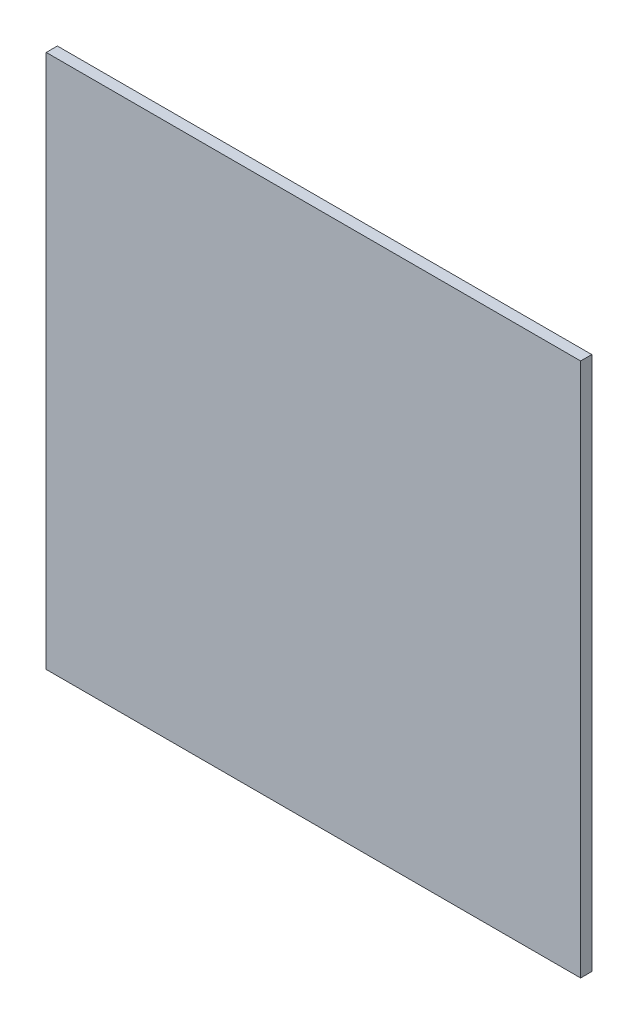
SolidWorks part; units mm, degrees
ref_plane "Front Plane" through (0, 0, 0) normal (0, 0, 1) x (1, 0, 0)
ref_plane "Top Plane" through (0, 0, 0) normal (0, 1, 0) x (1, 0, 0)
ref_plane "Right Plane" through (0, 0, 0) normal (1, 0, 0) x (0, 0, -1)
sketch "Sketch1" plane through (0, 0, 0) normal (0, 0, 1) x (1, 0, 0)
  line L1 (0, 0) -> (1219.2, 0)
  line L2 (0, 0) -> (0, -1219.2)
  line L3 (0, -1219.2) -> (1219.2, -1219.2)
  line L4 (1219.2, 0) -> (1219.2, -1219.2)
  dimension "D1" = 1219.2
  dimension "D2" = 1219.2
extrude "Boss-Extrude1" add sketch "Sketch1" along normal blind 25.4
